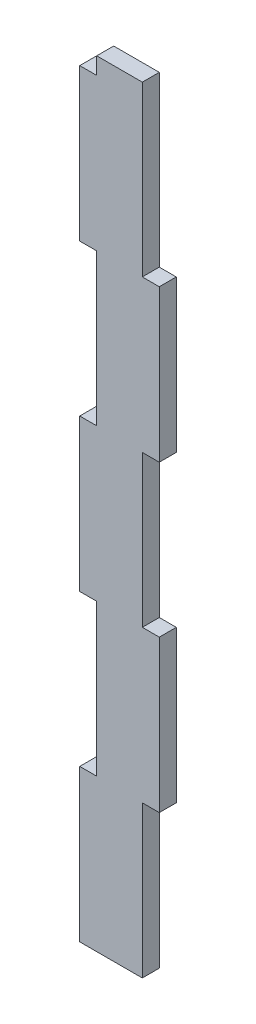
SolidWorks part; units mm, degrees
ref_plane "Front Plane" through (0, 0, 0) normal (0, 0, 1) x (1, 0, 0)
ref_plane "Top Plane" through (0, 0, 0) normal (0, 1, 0) x (1, 0, 0)
ref_plane "Right Plane" through (0, 0, 0) normal (1, 0, 0) x (0, 0, -1)
sketch "Sketch1" plane through (0, 0, 0) normal (0, 0, 1) x (1, 0, 0)
  line L1 (-239.3034, -13.9676) -> (-224.8784, -13.9676)
  line L2 (-239.3034, -13.9676) -> (-239.3034, -255.2926)
  line L3 (-239.3034, -255.2926) -> (-224.8784, -255.2926)
  line L4 (-224.8784, -13.9676) -> (-224.8784, -255.2926)
  line L5 (-239.3034, -13.9676) -> (-224.8784, -13.9676)
  line L6 (-239.3034, -13.9676) -> (-239.3034, -8.5676)
  line L7 (-239.3034, -8.5676) -> (-224.8784, -8.5676)
  line L8 (-224.8784, -13.9676) -> (-224.8784, -8.5676)
  line L29 (-239.3034, -110.4976) -> (-244.7034, -110.4976)
  line L30 (-239.3034, -13.9676) -> (-244.7034, -13.9676)
  line L31 (-239.3034, -13.9676) -> (-239.3034, -62.2326)
  line L32 (-239.3034, -62.2326) -> (-244.7034, -62.2326)
  line L33 (-244.7034, -13.9676) -> (-244.7034, -62.2326)
  line L34 (-244.7034, -110.4976) -> (-244.7034, -158.7626)
  line L35 (-239.3034, -158.7626) -> (-244.7034, -158.7626)
  line L36 (-239.3034, -207.0276) -> (-244.7034, -207.0276)
  line L37 (-244.7034, -207.0276) -> (-244.7034, -255.2926)
  line L38 (-239.3034, -255.2926) -> (-244.7034, -255.2926)
  line L39 (-224.8784, -158.7626) -> (-219.4784, -158.7626)
  line L40 (-224.8784, -62.2326) -> (-219.4784, -62.2326)
  line L41 (-224.8784, -62.2326) -> (-224.8784, -110.4976)
  line L42 (-224.8784, -110.4976) -> (-219.4784, -110.4976)
  line L43 (-219.4784, -62.2326) -> (-219.4784, -110.4976)
  line L44 (-219.4784, -158.7626) -> (-219.4784, -207.0276)
  line L45 (-224.8784, -207.0276) -> (-219.4784, -207.0276)
  dimension "D1" = 241.325
  dimension "D4" = 5.4
  dimension "D2" = 48.265
  dimension "D7" = 5.4
  dimension "D10" = 48.265
  dimension "D11" = 48.265
  dimension "D12" = 48.265
  dimension "D3" = 14.425
  dimension "D5" = 14.425
  dimension "D8" = 3
  dimension "D9" = 2
extrude "Boss-Extrude1" add sketch "Sketch1" along normal blind 5.4
sketch "Sketch2" plane through (0, 0, 5.4) normal (0, 0, 1) x (1, 0, 0)
  line L44 (-239.344, -8.5269) -> (-239.344, -13.9269)
  line L45 (-239.344, -13.9269) -> (-244.744, -13.9269)
  line L46 (-244.744, -13.9269) -> (-244.744, -62.2732)
  line L47 (-244.744, -62.2732) -> (-239.344, -62.2732)
  line L48 (-239.344, -62.2732) -> (-239.344, -110.4569)
  line L49 (-239.344, -110.4569) -> (-244.744, -110.4569)
  line L50 (-244.744, -110.4569) -> (-244.744, -158.8032)
  line L51 (-244.744, -158.8032) -> (-239.344, -158.8032)
  line L52 (-239.344, -158.8032) -> (-239.344, -206.9869)
  line L53 (-239.344, -206.9869) -> (-244.744, -206.9869)
  line L54 (-244.744, -206.9869) -> (-244.744, -255.3332)
  line L55 (-244.744, -255.3332) -> (-224.8377, -255.3332)
  line L56 (-224.8377, -255.3332) -> (-224.8377, -207.0682)
  line L57 (-224.8377, -207.0682) -> (-219.4377, -207.0682)
  line L58 (-219.4377, -207.0682) -> (-219.4377, -158.7219)
  line L59 (-219.4377, -158.7219) -> (-224.8377, -158.7219)
  line L60 (-224.8377, -158.7219) -> (-224.8377, -110.5382)
  line L61 (-224.8377, -110.5382) -> (-219.4377, -110.5382)
  line L62 (-219.4377, -110.5382) -> (-219.4377, -62.1919)
  line L63 (-219.4377, -62.1919) -> (-224.8377, -62.1919)
  line L64 (-224.8377, -62.1919) -> (-224.8377, -8.5269)
  line L65 (-224.8377, -8.5269) -> (-239.344, -8.5269)
  line L66 (-239.344, -8.5269) -> (-239.344, -13.9269)
  line L67 (-239.344, -13.9269) -> (-244.744, -13.9269)
  line L68 (-244.744, -13.9269) -> (-244.744, -62.2732)
  line L69 (-244.744, -62.2732) -> (-239.344, -62.2732)
  line L70 (-239.344, -62.2732) -> (-239.344, -110.4569)
  line L71 (-239.344, -110.4569) -> (-244.744, -110.4569)
  line L72 (-244.744, -110.4569) -> (-244.744, -158.8032)
  line L73 (-244.744, -158.8032) -> (-239.344, -158.8032)
  line L74 (-239.344, -158.8032) -> (-239.344, -206.9869)
  line L75 (-239.344, -206.9869) -> (-244.744, -206.9869)
  line L76 (-244.744, -206.9869) -> (-244.744, -255.3332)
  line L77 (-244.744, -255.3332) -> (-224.8377, -255.3332)
  line L78 (-224.8377, -255.3332) -> (-224.8377, -207.0682)
  line L79 (-224.8377, -207.0682) -> (-219.4377, -207.0682)
  line L80 (-219.4377, -207.0682) -> (-219.4377, -158.7219)
  line L81 (-219.4377, -158.7219) -> (-224.8377, -158.7219)
  line L82 (-224.8377, -158.7219) -> (-224.8377, -110.5382)
  line L83 (-224.8377, -110.5382) -> (-219.4377, -110.5382)
  line L84 (-219.4377, -110.5382) -> (-219.4377, -62.1919)
  line L85 (-219.4377, -62.1919) -> (-224.8377, -62.1919)
  line L86 (-224.8377, -62.1919) -> (-224.8377, -8.5269)
  line L87 (-224.8377, -8.5269) -> (-239.344, -8.5269)
  dimension "D1" = 0.0406
extrude "Boss-Extrude2" add sketch "Sketch2" against normal up to surface (5.4 mm away) up to face at (-233.2375, -123.1698, 0)
equation "\"Structure Height\"=24.1325"
equation "\"D1@Sketch1\"=\"Structure Height\""
equation "\"D2@Sketch1\"=\"Structure Height\"/5"
equation "\"D10@Sketch1\"=\"Structure Height\"/5"
equation "\"D11@Sketch1\"=\"Structure Height\"/5"
equation "\"D12@Sketch1\"=\"Structure Height\"/5"
